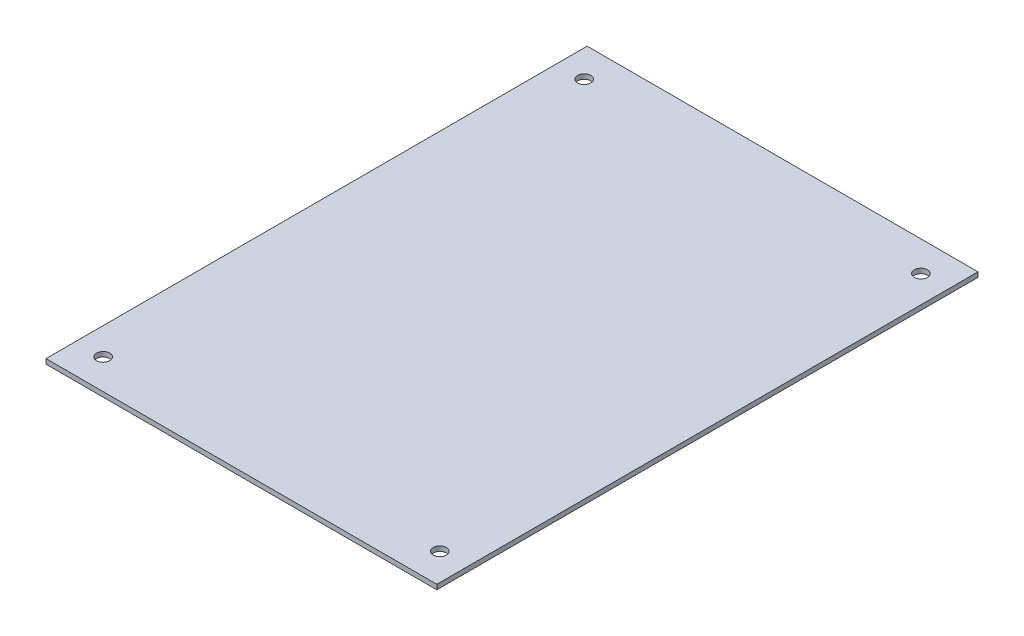
SolidWorks part; units mm, degrees
ref_plane "Front Plane" through (0, 0, 0) normal (0, 0, 1) x (1, 0, 0)
ref_plane "Top Plane" through (0, 0, 0) normal (0, 1, 0) x (1, 0, 0)
ref_plane "Right Plane" through (0, 0, 0) normal (1, 0, 0) x (0, 0, -1)
sketch "Sketch1" plane through (0, 0, 0) normal (0, 1, 0) x (1, 0, 0)
  line L0 (32.5, 0) -> (32.5, -13.3553)
  line L1 (0, 0) -> (65, 0)
  line L2 (0, 0) -> (0, 90)
  line L3 (0, 90) -> (65, 90)
  line L4 (65, 0) -> (65, 90)
  line L5 (0, 45) -> (-12.7347, 45)
  circle A0 centre (4.5, 5) radius 1.1
  circle A4 centre (4.5, 85) radius 1.1
  circle A5 centre (60.5, 5) radius 1.1
  circle A6 centre (60.5, 85) radius 1.1
  point P4 (32.5, 0)
  point P5 (0, 45)
  point P19 (0, 0)
  dimension "D3" = 2.2
  dimension "D4" = 28
  dimension "D1" = 90
  dimension "D2" = 65
  dimension "D5" = 40
extrude "Boss-Extrude1" add sketch "Sketch1" along normal blind 0.8 contours L1 L4 L3 L2 A6 A4 A0 A5
